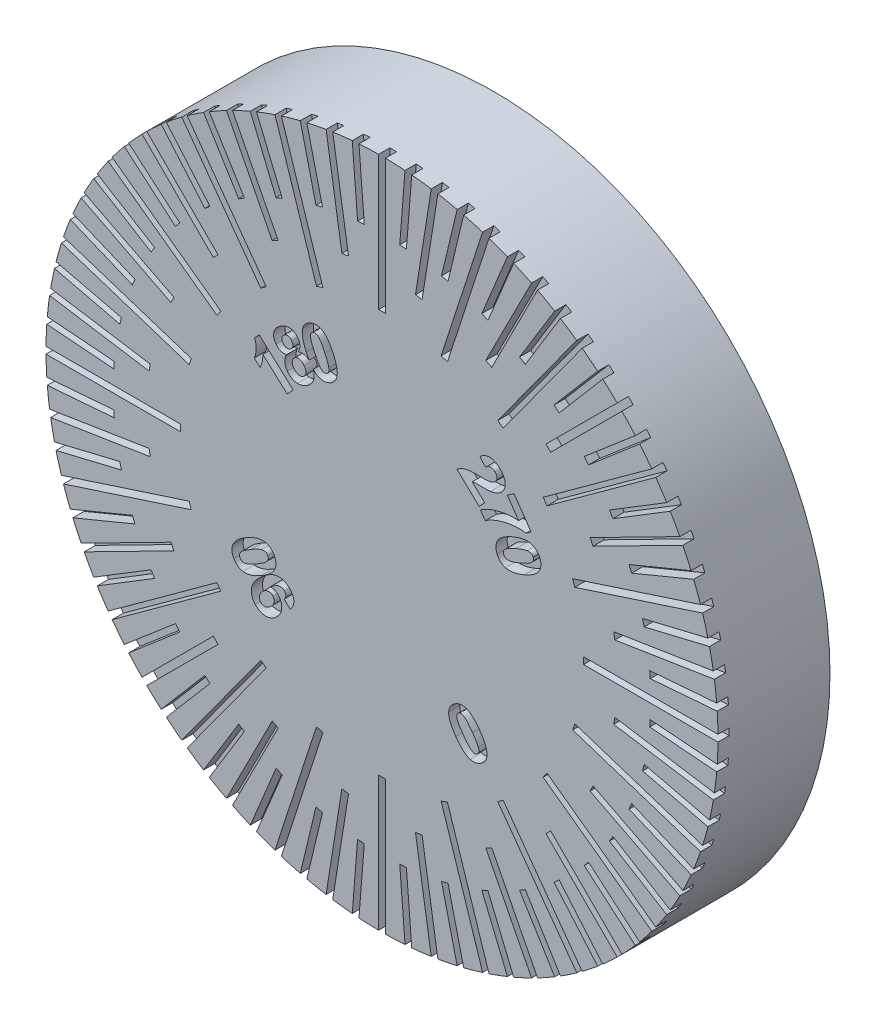
SolidWorks part; units mm, degrees
material "Acier S235"
ref_plane "Plan de face" through (0, 0, 0) normal (0, 0, 1) x (1, 0, 0)
ref_plane "Plan de dessus" through (0, 0, 0) normal (0, 1, 0) x (1, 0, 0)
ref_plane "Plan de droite" through (0, 0, 0) normal (1, 0, 0) x (0, 0, -1)
sketch "Esquisse1" plane through (0, 0, 0) normal (0, 0, 1) x (1, 0, 0)
  circle A0 centre (0, 0) radius 15
  dimension "D1" = 30
extrude "Boss.-Extru.1" add sketch "Esquisse1" along normal blind 5
sketch "Esquisse2" plane through (0, 0, 5) normal (0, 0, 1) x (1, 0, 0)
  line L0 (0, 15) -> (0, 9)
  line L1 (4.6353, 14.2658) -> (2.7812, 8.5595)
  line L2 (8.8168, 12.1353) -> (5.2901, 7.2812)
  line L3 (12.1353, 8.8168) -> (7.2812, 5.2901)
  line L4 (14.2658, 4.6353) -> (8.5595, 2.7812)
  line L5 (15, 0) -> (9, 0)
  line L6 (14.2658, -4.6353) -> (8.5595, -2.7812)
  line L7 (12.1353, -8.8168) -> (7.2812, -5.2901)
  line L8 (8.8168, -12.1353) -> (5.2901, -7.2812)
  line L9 (4.6353, -14.2658) -> (2.7812, -8.5595)
  line L10 (0, -15) -> (0, -9)
  line L11 (-4.6353, -14.2658) -> (-2.7812, -8.5595)
  line L12 (-8.8168, -12.1353) -> (-5.2901, -7.2812)
  line L13 (-12.1353, -8.8168) -> (-7.2812, -5.2901)
  line L14 (-14.2658, -4.6353) -> (-8.5595, -2.7812)
  line L15 (-15, 0) -> (-9, 0)
  line L16 (-14.2658, 4.6353) -> (-8.5595, 2.7812)
  line L17 (-12.1353, 8.8168) -> (-7.2812, 5.2901)
  line L18 (-8.8168, 12.1353) -> (-5.2901, 7.2812)
  line L19 (-4.6353, 14.2658) -> (-2.7812, 8.5595)
  circle A0 centre (0, 0) radius 15 construction
  point P46 (0, 0)
  dimension "D1" = 6
  dimension "D2" = 20
sketch "Esquisse3" plane through (0, 0, 5) normal (0, 0, 1) x (1, 0, 0)
  line L0 (1.1769, 14.9538) -> (0.9415, 11.963)
  line L1 (1.1769, 14.9538) -> (0, 0) construction
  line L3 (0, 15) -> (0, 9) construction
  line L4 (3.5017, 14.5855) -> (2.8013, 11.6684)
  line L5 (5.7403, 13.8582) -> (4.5922, 11.0866)
  line L6 (7.8375, 12.7896) -> (6.27, 10.2317)
  line L7 (9.7417, 11.4061) -> (7.7934, 9.1249)
  line L8 (11.4061, 9.7417) -> (9.1249, 7.7934)
  line L9 (12.7896, 7.8375) -> (10.2317, 6.27)
  line L10 (13.8582, 5.7403) -> (11.0866, 4.5922)
  line L11 (14.5855, 3.5017) -> (11.6684, 2.8013)
  line L12 (14.9538, 1.1769) -> (11.963, 0.9415)
  line L13 (14.9538, -1.1769) -> (11.963, -0.9415)
  line L14 (14.5855, -3.5017) -> (11.6684, -2.8013)
  line L15 (13.8582, -5.7403) -> (11.0866, -4.5922)
  line L16 (12.7896, -7.8375) -> (10.2317, -6.27)
  line L17 (11.4061, -9.7417) -> (9.1249, -7.7934)
  line L18 (9.7417, -11.4061) -> (7.7934, -9.1249)
  line L19 (7.8375, -12.7896) -> (6.27, -10.2317)
  line L20 (5.7403, -13.8582) -> (4.5922, -11.0866)
  line L21 (3.5017, -14.5855) -> (2.8013, -11.6684)
  line L22 (1.1769, -14.9538) -> (0.9415, -11.963)
  line L23 (-1.1769, -14.9538) -> (-0.9415, -11.963)
  line L24 (-3.5017, -14.5855) -> (-2.8013, -11.6684)
  line L25 (-5.7403, -13.8582) -> (-4.5922, -11.0866)
  line L26 (-7.8375, -12.7896) -> (-6.27, -10.2317)
  line L27 (-9.7417, -11.4061) -> (-7.7934, -9.1249)
  line L28 (-11.4061, -9.7417) -> (-9.1249, -7.7934)
  line L29 (-12.7896, -7.8375) -> (-10.2317, -6.27)
  line L30 (-13.8582, -5.7403) -> (-11.0866, -4.5922)
  line L31 (-14.5855, -3.5017) -> (-11.6684, -2.8013)
  line L32 (-14.9538, -1.1769) -> (-11.963, -0.9415)
  line L33 (-14.9538, 1.1769) -> (-11.963, 0.9415)
  line L34 (-14.5855, 3.5017) -> (-11.6684, 2.8013)
  line L35 (-13.8582, 5.7403) -> (-11.0866, 4.5922)
  line L36 (-12.7896, 7.8375) -> (-10.2317, 6.27)
  line L37 (-11.4061, 9.7417) -> (-9.1249, 7.7934)
  line L38 (-9.7417, 11.4061) -> (-7.7934, 9.1249)
  line L39 (-7.8375, 12.7896) -> (-6.27, 10.2317)
  line L40 (-5.7403, 13.8582) -> (-4.5922, 11.0866)
  line L41 (-3.5017, 14.5855) -> (-2.8013, 11.6684)
  line L42 (-1.1769, 14.9538) -> (-0.9415, 11.963)
  line L43 (2.3465, 14.8153) -> (1.6426, 10.3707)
  line L44 (2.3465, 14.8153) -> (0, 0) construction
  line L46 (6.8099, 13.3651) -> (4.7669, 9.3556)
  line L47 (10.6066, 10.6066) -> (7.4246, 7.4246)
  line L48 (13.3651, 6.8099) -> (9.3556, 4.7669)
  line L49 (14.8153, 2.3465) -> (10.3707, 1.6426)
  line L50 (14.8153, -2.3465) -> (10.3707, -1.6426)
  line L51 (13.3651, -6.8099) -> (9.3556, -4.7669)
  line L52 (10.6066, -10.6066) -> (7.4246, -7.4246)
  line L53 (6.8099, -13.3651) -> (4.7669, -9.3556)
  line L54 (2.3465, -14.8153) -> (1.6426, -10.3707)
  line L55 (-2.3465, -14.8153) -> (-1.6426, -10.3707)
  line L56 (-6.8099, -13.3651) -> (-4.7669, -9.3556)
  line L57 (-10.6066, -10.6066) -> (-7.4246, -7.4246)
  line L58 (-13.3651, -6.8099) -> (-9.3556, -4.7669)
  line L59 (-14.8153, -2.3465) -> (-10.3707, -1.6426)
  line L60 (-14.8153, 2.3465) -> (-10.3707, 1.6426)
  line L61 (-13.3651, 6.8099) -> (-9.3556, 4.7669)
  line L62 (-10.6066, 10.6066) -> (-7.4246, 7.4246)
  line L63 (-6.8099, 13.3651) -> (-4.7669, 9.3556)
  line L64 (-2.3465, 14.8153) -> (-1.6426, 10.3707)
  circle A1 centre (0, 0) radius 15 construction
  point P89 (0, 0)
  point P131 (0, 0)
  dimension "D1" = 3
  dimension "D2" = 4.5
  dimension "D4" = 4.5
  dimension "D5" = 4.5
  dimension "D6" = 20
  dimension "D3" = 40
sketch "Esquisse4" plane through (0, 0, 5) normal (0, 0, 1) x (1, 0, 0)
  circle A0 centre (0, 0) radius 5.6756 construction
  text T0 "0                   90                180               270    " font "Arial" height in points 8
extrude "Enlèv. de mat.-Extru.-Mince1" cut sketch "Esquisse2" along direction (0, 0, 1) on the side against the normal blind 0.5 thin contours L17 thin type mid plane wall 0.3
extrude "Enlèv. de mat.-Extru.-Mince2" cut sketch "Esquisse3" against normal blind 0.5 thin thin type mid plane wall 0.3
extrude "Enlèv. mat.-Extru.1" cut sketch "Esquisse4" against normal blind 0.5
